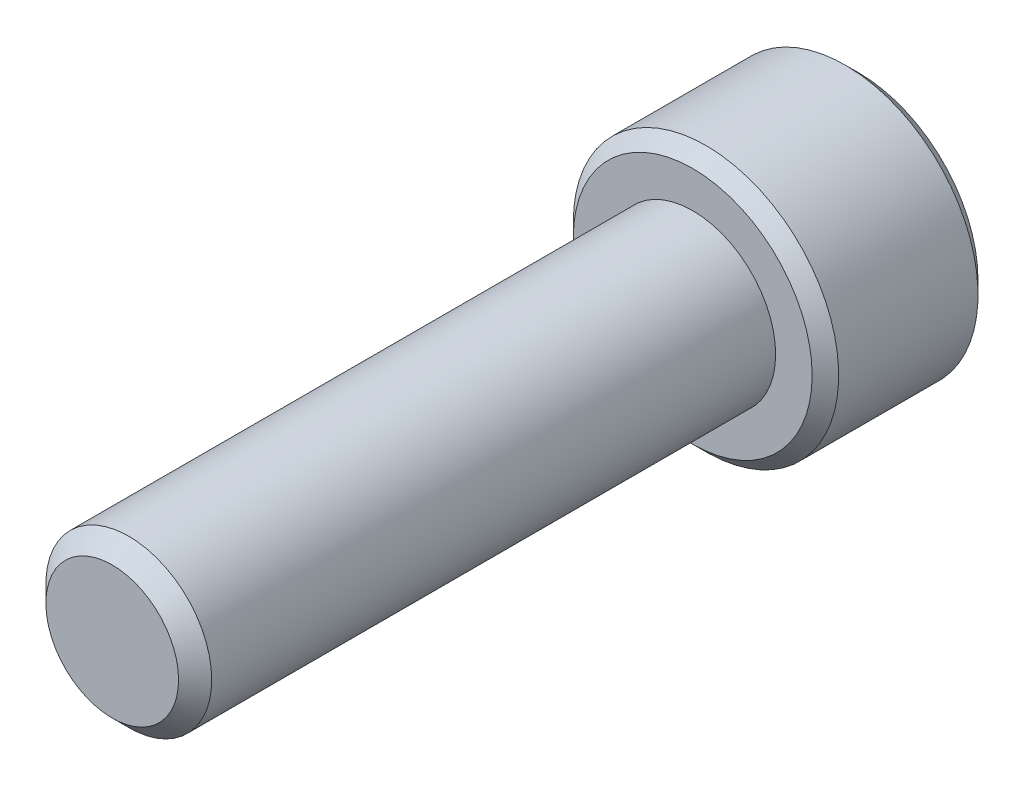
SolidWorks part; units mm, degrees
material "18-8 SSTL"
ref_plane "Front Plane" through (0, 0, 0) normal (0, 0, 1) x (1, 0, 0)
ref_plane "Top Plane" through (0, 0, 0) normal (0, 1, 0) x (1, 0, 0)
ref_plane "Right Plane" through (0, 0, 0) normal (1, 0, 0) x (0, 0, -1)
sketch "Sketch1" plane through (0, 0, 0) normal (0, 0, 1) x (1, 0, 0)
  circle A0 centre (0, 0) radius 5
  dimension "OD" = 10
extrude "Extrude1" add sketch "Sketch1" against normal blind 35
cosmetic thread "Cosmetic Thread1" parameters "D2"=9
sketch "Sketch6" plane through (0, 0, -35) normal (0, 0, -1) x (-1, 0, 0)
  circle A0 centre (0, 0) radius 8
  dimension "head dia" = 16
extrude "Extrude2" add sketch "Sketch6" along normal blind 10
sketch "Sketch7" plane through (0, 0, -45) normal (0, 0, -1) x (-1, 0, 0)
  line L1 (0, 4.6188) -> (-4, 2.3094)
  line L2 (-4, 2.3094) -> (-4, -2.3094)
  line L3 (-4, -2.3094) -> (0, -4.6188)
  line L4 (0, -4.6188) -> (4, -2.3094)
  line L5 (4, -2.3094) -> (4, 2.3094)
  line L6 (4, 2.3094) -> (0, 4.6188)
  circle A0 centre (0, 0) radius 4 construction
  dimension "hex dia" = 8
extrude "Cut-Extrude1" cut sketch "Sketch7" against normal blind 6
sketch "Sketch8" plane through (0, 0, -45) normal (0, 0, -1) x (-1, 0, 0)
  circle A0 centre (0, 0) radius 4.6188
extrude "Cut-Extrude2" cut sketch "Sketch8" against normal through all draft 45
chamfer "Chamfer1" distance 0.8 angle 45 2 edges at (-8, 0, -45) (-8, 0, -35)
chamfer "Chamfer2" distance 1 angle 45 1 edges at (5, 0, 0)
